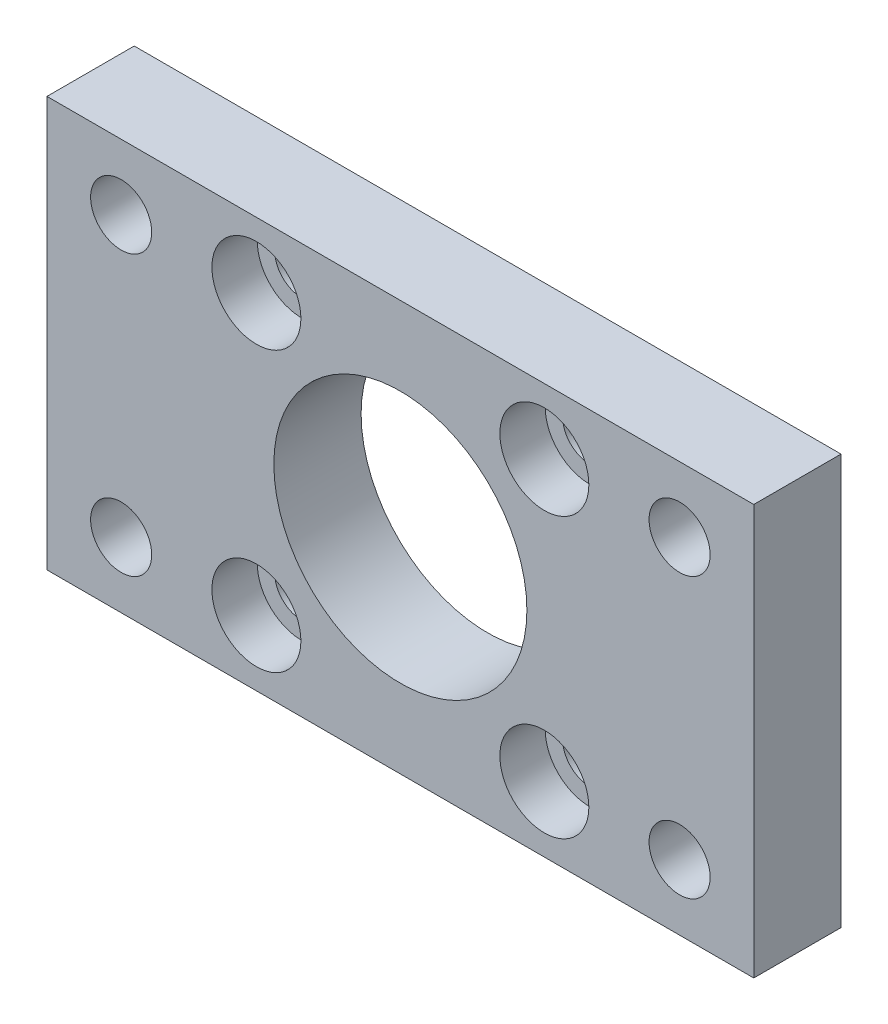
SolidWorks part; units mm, degrees
ref_plane "Plan de face" through (0, 0, 0) normal (0, 0, 1) x (1, 0, 0)
ref_plane "Plan de dessus" through (0, 0, 0) normal (0, 1, 0) x (1, 0, 0)
ref_plane "Plan de droite" through (0, 0, 0) normal (1, 0, 0) x (0, 0, -1)
sketch "Esquisse1" plane through (0, 0, 0) normal (0, 0, 1) x (1, 0, 0)
  line L0 (0, 23.5) -> (81, 23.5) construction
  line L1 (0, 0) -> (81, 0)
  line L2 (0, 0) -> (0, 47)
  line L3 (0, 47) -> (81, 47)
  line L4 (81, 0) -> (81, 47)
  line L5 (40.5, 47) -> (40.5, 0) construction
  line L7 (72.5, 7.5) -> (8.5, 7.5) construction
  line L8 (72.5, 7.5) -> (72.5, 39.5) construction
  line L9 (72.5, 39.5) -> (8.5, 39.5) construction
  line L10 (8.5, 7.5) -> (8.5, 39.5) construction
  line L11 (72.5, 7.5) -> (8.5, 39.5) construction
  line L12 (72.5, 39.5) -> (8.5, 7.5) construction
  circle A0 centre (40.5, 23.5) radius 14.5
  circle A1 centre (8.5, 39.5) radius 3.5
  circle A2 centre (72.5, 39.5) radius 3.5
  circle A3 centre (72.5, 7.5) radius 3.5
  circle A4 centre (8.5, 7.5) radius 3.5
  circle A5 centre (24, 39.5) radius 3.1
  circle A6 centre (57, 39.5) radius 3.1
  circle A7 centre (57, 7.5) radius 3.1
  circle A8 centre (24, 7.5) radius 3.1
  dimension "D1" = 29
  dimension "D6" = 16.5
  dimension "D2" = 81
  dimension "D3" = 47
  dimension "D4" = 32
  dimension "D5" = 64
sketch "Esquisse2" plane through (0, 0, 0) normal (0, 0, 1) x (1, 0, 0)
  line L0 (0, 23.5) -> (81, 23.5) construction
  line L1 (0, 0) -> (81, 0)
  line L2 (0, 0) -> (0, 47)
  line L3 (0, 47) -> (81, 47)
  line L4 (81, 0) -> (81, 47)
  line L5 (40.5, 47) -> (40.5, 0) construction
  line L6 (72.5, 7.5) -> (8.5, 7.5) construction
  line L7 (72.5, 7.5) -> (72.5, 39.5) construction
  line L8 (72.5, 39.5) -> (8.5, 39.5) construction
  line L9 (8.5, 7.5) -> (8.5, 39.5) construction
  line L10 (72.5, 7.5) -> (8.5, 39.5) construction
  line L11 (72.5, 39.5) -> (8.5, 7.5) construction
  circle A0 centre (40.5, 23.5) radius 14.5
  circle A1 centre (8.5, 39.5) radius 3.5
  circle A2 centre (72.5, 39.5) radius 3.5
  circle A3 centre (72.5, 7.5) radius 3.5
  circle A4 centre (8.5, 7.5) radius 3.5
  circle A5 centre (24, 39.5) radius 3.1
  circle A6 centre (57, 39.5) radius 3.1
  circle A7 centre (57, 7.5) radius 3.1
  circle A8 centre (24, 7.5) radius 3.1
  dimension "D1" = 64
  dimension "D2" = 16.5
extrude "Boss.-Extru.1" add sketch "Esquisse2" along normal blind 10
sketch "Esquisse3" plane through (0, 0, 10) normal (0, 0, 1) x (1, 0, 0)
  circle A0 centre (24, 39.5) radius 5.1
  circle A1 centre (24, 7.5) radius 5.1
  circle A2 centre (57, 7.5) radius 5.1
  circle A3 centre (57, 39.5) radius 5.1
  dimension "D1" = 10.2
  dimension "D2" = 10.2
  dimension "D3" = 10.2
sketch "Esquisse5" plane through (0, 0, 10) normal (0, 0, 1) x (1, 0, 0)
  circle A0 centre (24, 39.5) radius 5.1
  circle A1 centre (24, 7.5) radius 5.1
  circle A2 centre (57, 7.5) radius 5.1
  circle A3 centre (57, 39.5) radius 5.1
extrude "Enlèv. mat.-Extru.1" cut sketch "Esquisse5" against normal blind 5.2
